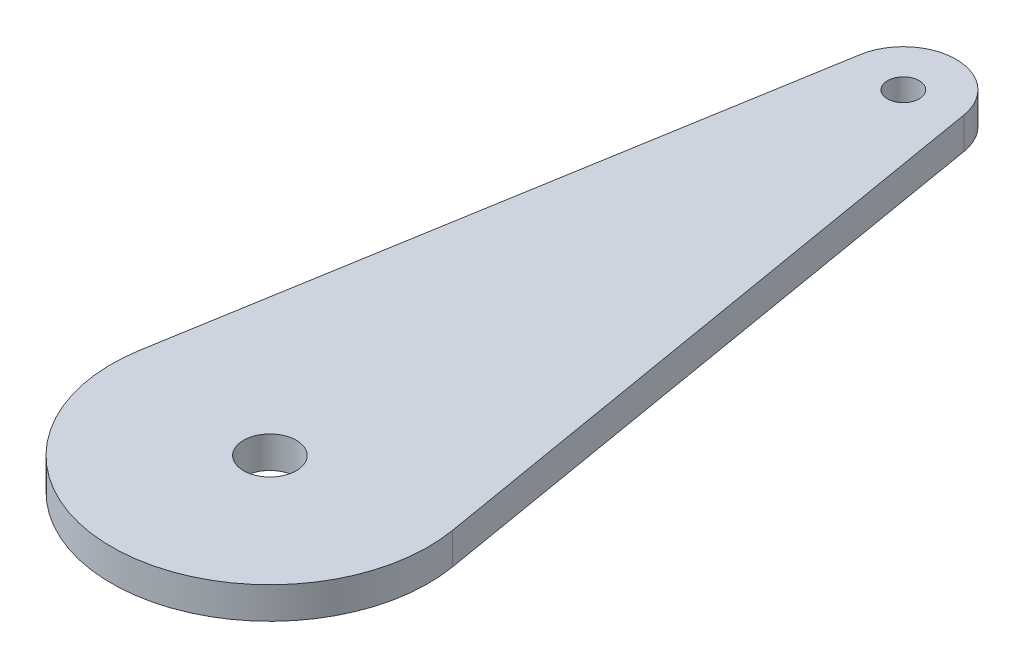
SolidWorks part; units mm, degrees
ref_plane "Front Plane" through (0, 0, 0) normal (0, 0, 1) x (1, 0, 0)
ref_plane "Top Plane" through (0, 0, 0) normal (0, 1, 0) x (1, 0, 0)
ref_plane "Right Plane" through (0, 0, 0) normal (1, 0, 0) x (0, 0, -1)
sketch "Sketch1" plane through (0, 0, 0) normal (0, 1, 0) x (1, 0, 0)
  line L1 (-4.9301, 60.8333) -> (-14.7902, 2.5)
  line L2 (14.7902, 2.5) -> (4.9301, 60.8333)
  arc A0 (-14.7902, 2.5) -> (14.7902, 2.5) centre (0, 0) ccw
  arc A1 (4.9301, 60.8333) -> (-4.9301, 60.8333) centre (0, 60) ccw
  circle A2 centre (0, 60) radius 1.5
extrude "Boss-Extrude1" add sketch "Sketch1" along normal blind 3
sketch "Sketch2" plane through (0, 3, 0) normal (0, 1, 0) x (1, 0, 0)
  circle A0 centre (0, 0) radius 2.5
extrude "Cut-Extrude1" cut sketch "Sketch2" against normal blind 3
